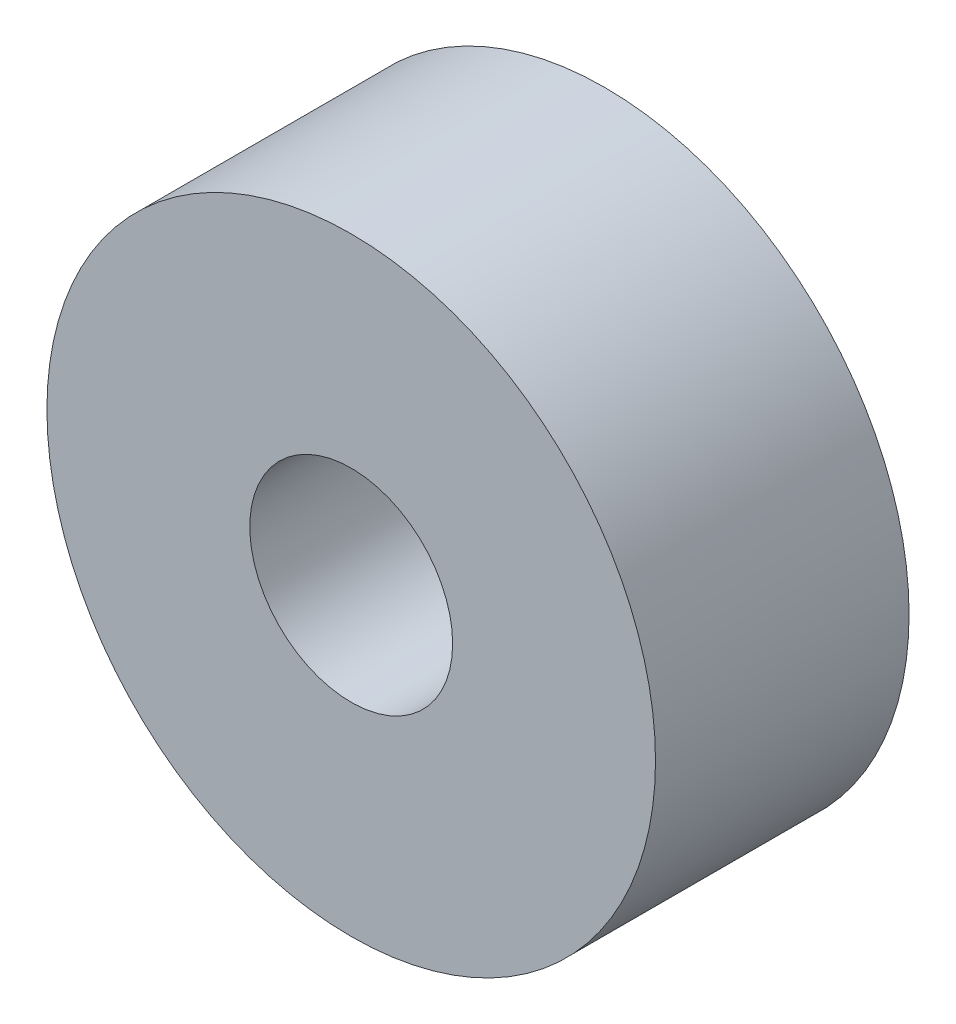
SolidWorks part; units mm, degrees
ref_plane "Front Plane" through (0, 0, 0) normal (0, 0, 1) x (1, 0, 0)
ref_plane "Top Plane" through (0, 0, 0) normal (0, 1, 0) x (1, 0, 0)
ref_plane "Right Plane" through (0, 0, 0) normal (1, 0, 0) x (0, 0, -1)
sketch "Sketch1" plane through (0, 0, 0) normal (0, 0, 1) x (1, 0, 0)
  circle A0 centre (0, 0) radius 4.7625
  dimension "D1" = 9.525
extrude "Extrude1" add sketch "Sketch1" along normal blind 3.9688
sketch "Sketch2" plane through (0, 0, 3.9688) normal (0, 0, 1) x (1, 0, 0)
  circle A0 centre (0, 0) radius 1.5875
  dimension "D1" = 3.175
extrude "Extrude2" cut sketch "Sketch2" against normal through all
